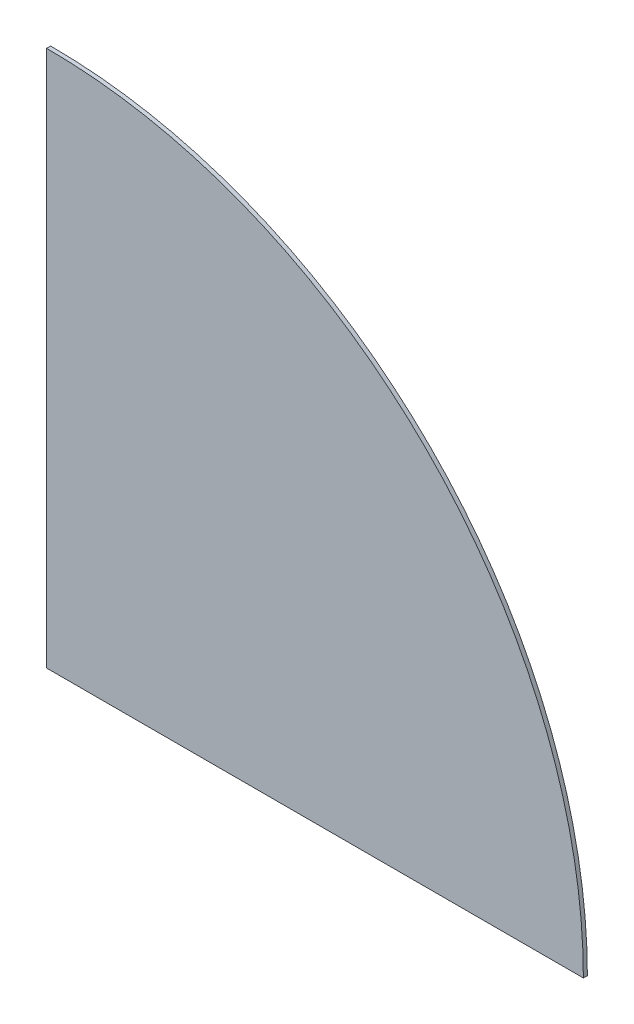
SolidWorks part; units mm, degrees
material "pcb"
ref_plane "Front Plane" through (0, 0, 0) normal (0, 0, 1) x (1, 0, 0)
ref_plane "Top Plane" through (0, 0, 0) normal (0, 1, 0) x (1, 0, 0)
ref_plane "Right Plane" through (0, 0, 0) normal (1, 0, 0) x (0, 0, -1)
sketch "Sketch1" plane through (0, 0, 0) normal (0, 0, 1) x (1, 0, 0)
  line L1 (-31, -334) -> (-165.4084, -334)
  line L2 (-165.4084, -334) -> (-165.4084, -199.5916)
  arc A0 (-165.4084, -199.5916) -> (-31, -334) centre (-165.4084, -334) cw
extrude "Boss-Extrude1" add sketch "Sketch1" along normal blind 1 contours A0 L1 L2
